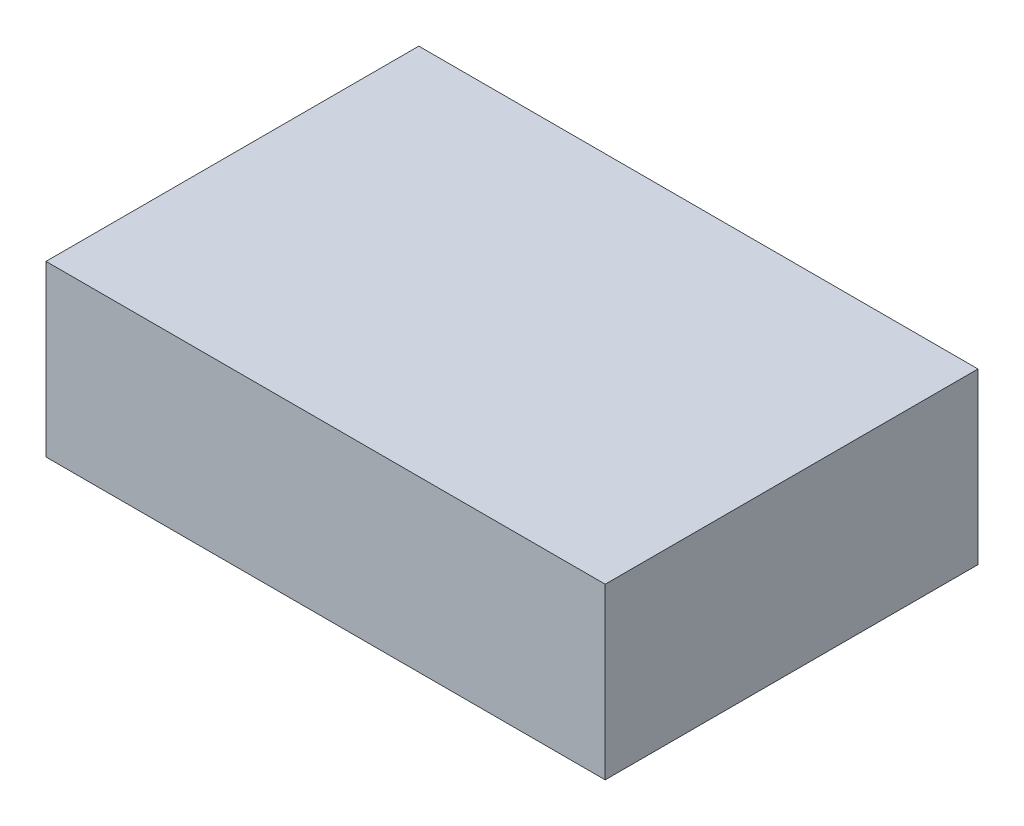
SolidWorks part; units mm, degrees
ref_plane "Front Plane" through (0, 0, 0) normal (0, 0, 1) x (1, 0, 0)
ref_plane "Top Plane" through (0, 0, 0) normal (0, 1, 0) x (1, 0, 0)
ref_plane "Right Plane" through (0, 0, 0) normal (1, 0, 0) x (0, 0, -1)
sketch "Sketch1" plane through (0, 0, 0) normal (0, 1, 0) x (1, 0, 0)
  line L1 (-33, -22) -> (33, -22)
  line L2 (-33, -22) -> (-33, 22)
  line L3 (-33, 22) -> (33, 22)
  line L4 (33, -22) -> (33, 22)
  line L5 (-33, -22) -> (33, 22) construction
  line L6 (-33, 22) -> (33, -22) construction
  point P0 (0, 0)
extrude "Boss-Extrude1" add sketch "Sketch1" along normal blind 20
